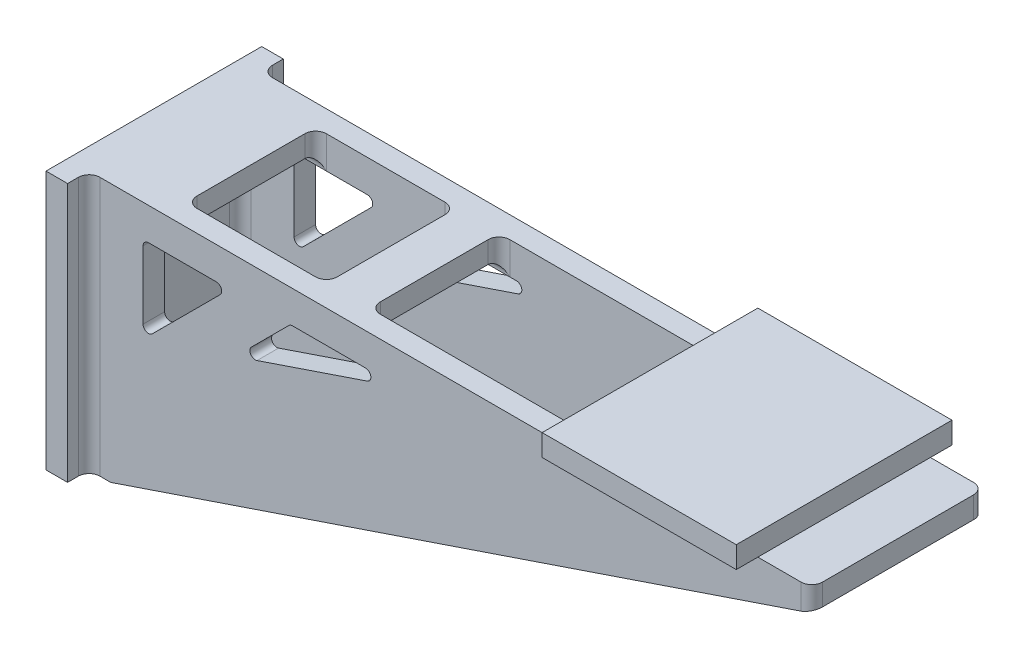
SolidWorks part; units mm, degrees
ref_plane "Front Plane" through (0, 0, 0) normal (0, 0, 1) x (1, 0, 0)
ref_plane "Top Plane" through (0, 0, 0) normal (0, 1, 0) x (1, 0, 0)
ref_plane "Right Plane" through (0, 0, 0) normal (1, 0, 0) x (0, 0, -1)
sketch "Base Sketch" plane through (0, 0, 0) normal (1, 0, 0) x (0, 0, -1)
  line L1 (-127, -152.4) -> (127, -152.4)
  line L2 (-127, -152.4) -> (-127, 152.4)
  line L3 (-127, 152.4) -> (127, 152.4)
  line L4 (127, -152.4) -> (127, 152.4)
  line L5 (-127, -152.4) -> (127, 152.4) construction
  line L6 (-127, 152.4) -> (127, -152.4) construction
  point P0 (0, 0)
  dimension "D1" = 304.8
  dimension "D2" = 254
extrude "Base" add sketch "Base Sketch" along normal blind 25.4
ref_plane "Right Triangle Plane" through (0, 0, 101.6) normal (0, 0, 1) x (1, 0, 0)
sketch "Right Triangle Sketch" plane through (0, 0, 101.6) normal (0, 0, 1) x (1, 0, 0)
  line L0 (0, 152.4) -> (876.3, 152.4)
  line L1 (876.3, 152.4) -> (876.3, 127)
  line L2 (876.3, 127) -> (50.8, -152.4)
  line L3 (50.8, -152.4) -> (0, -152.4)
  line L4 (0, -152.4) -> (0, 152.4)
  dimension "D1" = 876.3
  dimension "D2" = 25.4
  dimension "D3" = 50.8
extrude "Right Triangle" add sketch "Right Triangle Sketch" against normal blind 25.4
ref_plane "Left Triangle Plane" through (0, 0, -101.6) normal (0, 0, -1) x (-1, 0, 0)
sketch "Left Triangle Sketch" plane through (0, 0, -101.6) normal (0, 0, -1) x (-1, 0, 0)
  line L0 (0, 152.4) -> (-876.3, 152.4)
  line L1 (-876.3, 152.4) -> (-876.3, 127)
  line L2 (-876.3, 127) -> (-50.8, -152.4)
  line L3 (-50.8, -152.4) -> (0, -152.4)
  line L4 (0, -152.4) -> (0, 152.4)
extrude "Left Triangle" add sketch "Left Triangle Sketch" against normal blind 25.4
sketch "Support Beams Sketch" plane through (0, 152.4, 0) normal (0, 1, 0) x (1, 0, 0)
  line L0 (13.97, 101.6) -> (-13.97, 101.6) construction
  line L1 (0, 101.6) -> (114.3, 101.6)
  line L2 (0, 101.6) -> (0, -101.6)
  line L3 (0, -101.6) -> (114.3, -101.6)
  line L4 (114.3, 101.6) -> (114.3, -101.6)
  line L5 (0, 127) -> (0, -127) construction
  line L6 (876.3, -101.6) -> (25.4, -101.6) construction
  line L7 (25.4, 76.2) -> (25.4, -76.2) construction
  line L8 (25.4, 101.6) -> (876.3, 101.6) construction
  line L9 (279.4, 101.6) -> (330.2, 101.6)
  line L10 (279.4, 101.6) -> (279.4, -101.6)
  line L11 (279.4, -101.6) -> (330.2, -101.6)
  line L12 (330.2, 101.6) -> (330.2, -101.6)
  line L14 (787.4, 101.6) -> (876.3, 101.6)
  line L15 (787.4, 101.6) -> (787.4, -101.6)
  line L16 (787.4, -101.6) -> (876.3, -101.6)
  line L17 (876.3, 101.6) -> (876.3, -101.6)
  dimension "D1" = 88.9
  dimension "D2" = 254
  dimension "D3" = 304.8
  dimension "D4" = 762
  dimension "D5" = 850.9
extrude "Support Beams" add sketch "Support Beams Sketch" against normal blind 25.4
fillet "Fillet1" radius 12.7 21 edges at (25.4, 0, -101.6) (25.4, 0, 101.6) (25.4, -12.7, -76.2) (69.85, 127, -76.2) (25.4, 127, 0) (25.4, -12.7, 76.2) (69.85, 127, 76.2) (304.8, 127, 76.2) (304.8, 127, -76.2) (831.85, 127, -76.2) (831.85, 127, 76.2) (787.4, 139.7, 76.2) (787.4, 139.7, -76.2) (279.4, 139.7, 76.2) (279.4, 139.7, -76.2) (330.2, 139.7, -76.2) (330.2, 139.7, 76.2) (114.3, 139.7, 76.2) (114.3, 139.7, -76.2) (876.3, 139.7, -101.6) (876.3, 139.7, 101.6)
sketch "Top Plate Sketch" plane through (0, 152.4, 0) normal (0, 1, 0) x (1, 0, 0)
  line L0 (25.4, 127) -> (25.4, 114.3) construction
  line L1 (584.2, 127) -> (812.8, 127)
  line L2 (584.2, 127) -> (584.2, -127)
  line L3 (584.2, -127) -> (812.8, -127)
  line L4 (812.8, 127) -> (812.8, -127)
  line L5 (38.1, 101.6) -> (863.6, 101.6) construction
  point P6 (25.4, 120.65)
  dimension "D1" = 558.8
  dimension "D2" = 787.4
  dimension "D3" = 254
  dimension "D4" = 25.4
extrude "Top Plate" add sketch "Top Plate Sketch" along normal blind 25.4
fillet "Fillet4" radius 2.54 5 edges at (679.45, 152.4, -76.2) (783.6803, 152.4, -72.4803) (679.45, 152.4, 76.2) (783.6803, 152.4, 72.4803) (787.4, 152.4, 0)
sketch "Sketch1" plane through (0, 0, 101.6) normal (0, 0, 1) x (1, 0, 0)
  line L0 (88.9, 12.7) -> (88.9, 114.3)
  line L1 (88.9, 114.3) -> (190.5, 114.3)
  line L2 (190.5, 114.3) -> (88.9, 12.7)
  line L3 (197.3653, 49.3233) -> (262.342, 114.3)
  line L4 (262.342, 114.3) -> (389.342, 114.3)
  line L5 (389.342, 114.3) -> (197.3653, 49.3233)
  line L7 (25.4, 152.4) -> (25.4, -152.4) construction
  line L8 (584.2, 152.4) -> (38.1, 152.4) construction
  line L9 (50.8, -152.4) -> (863.6, 122.7015) construction
  dimension "D1" = 63.5
  dimension "D2" = 38.1
  dimension "D3" = 101.6
  dimension "D4" = 101.6
  dimension "D5" = 50.8
  dimension "D6" = 127
extrude "Cut-Extrude1" cut sketch "Sketch1" against normal through all
fillet "Fillet6" radius 6.35 12 edges at (389.342, 114.3, -88.9) (262.342, 114.3, -88.9) (197.3653, 49.3233, -88.9) (190.5, 114.3, -88.9) (88.9, 12.7, -88.9) (88.9, 114.3, -88.9) (88.9, 114.3, 88.9) (88.9, 12.7, 88.9) (190.5, 114.3, 88.9) (197.3653, 49.3233, 88.9) (262.342, 114.3, 88.9) (389.342, 114.3, 88.9)
